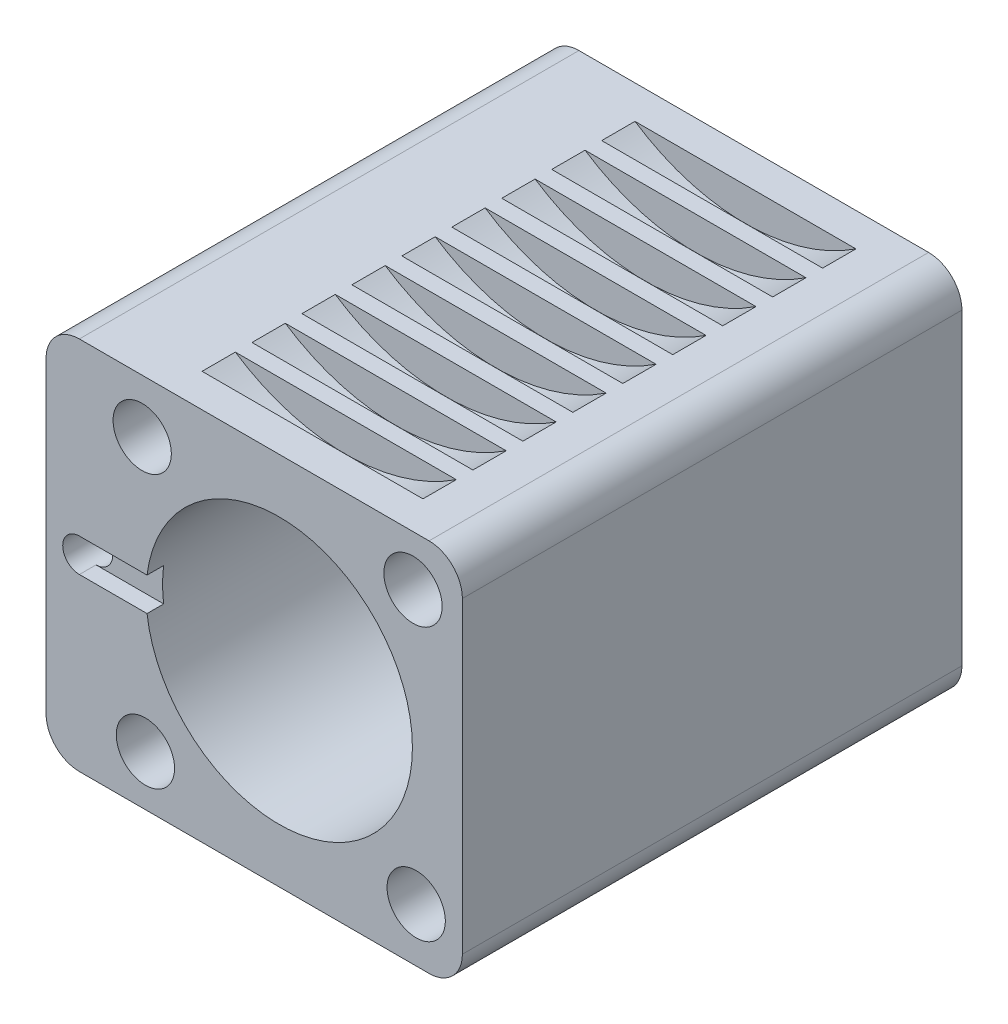
SolidWorks part; units mm, degrees
ref_plane "Front Plane" through (0, 0, 0) normal (0, 0, 1) x (1, 0, 0)
ref_plane "Top Plane" through (0, 0, 0) normal (0, 1, 0) x (1, 0, 0)
ref_plane "Right Plane" through (0, 0, 0) normal (1, 0, 0) x (0, 0, -1)
sketch "Sketch1" plane through (0, 0, 0) normal (0, 0, 1) x (1, 0, 0)
  line L0 (0, 0) -> (20.8284, 21.3284) construction
  line L1 (-24, 22.5) -> (18, 22.5)
  line L2 (-28, 18.5) -> (-28, -18.5)
  line L3 (-24, -22.5) -> (18, -22.5)
  line L4 (22, 18.5) -> (22, -18.5)
  arc A1 (-28, -18.5) -> (-24, -22.5) centre (-24, -18.5) ccw
  arc A2 (18, -22.5) -> (22, -18.5) centre (18, -18.5) ccw
  arc A3 (18, 22.5) -> (22, 18.5) centre (18, 18.5) cw
  arc A4 (-24, 22.5) -> (-28, 18.5) centre (-24, 18.5) ccw
  circle A5 centre (0, 0) radius 16
  circle A6 centre (0, 0) radius 23 construction
  circle A7 centre (16.0694, 16.4552) radius 3.5
  circle A8 centre (16.4552, -16.0694) radius 3.5
  circle A9 centre (-16.0694, -16.4552) radius 3.5
  circle A10 centre (-16.4552, 16.0694) radius 3.5
  circle A11 centre (-24, 0) radius 2
  point P4 (22, 0)
  point P9 (-28, -22.5)
  point P14 (22, 22.5)
  point P17 (-28, 22.5)
  point P33 (0, 0)
  dimension "D3" = 22
  dimension "D4" = 4
  dimension "D5" = 32
  dimension "D6" = 46
  dimension "D7" = 7
  dimension "D10" = 4
  dimension "D1" = 45
  dimension "D2" = 50
  dimension "D9" = 24
  dimension "D8" = 4
extrude "Boss-Extrude1" add sketch "Sketch1" along normal blind 60
sketch "Sketch2" plane through (0, 0, 0) normal (0, 0, -1) x (-1, 0, 0)
  circle A0 centre (0, 0) radius 18
  circle A1 centre (0, 0) radius 16 construction
  circle A2 centre (0, 0) radius 16
  dimension "D1" = 36
extrude "Boss-Extrude2" add sketch "Sketch2" along normal blind 2
sketch "Sketch3" plane through (0, 0, 60) normal (0, 0, 1) x (1, 0, 0)
  line L1 (-15.8745, -2) -> (-24, -2)
  line L3 (-15.8745, 2) -> (-24, 2)
  line L4 (-24, -2) -> (-24, 2)
  circle A0 centre (-24, 0) radius 2 construction
  circle A1 centre (0, 0) radius 16 construction
  circle A2 centre (0, 0) radius 16
  arc A3 (-15.8745, -2) -> (-15.8745, 2) centre (0, 0) cw
  circle M8 centre (-24, 0) radius 2
  circle M9 centre (0, 0) radius 16
  dimension "D1" = 4
extrude "Cut-Extrude1" cut sketch "Sketch3" against normal blind 2 contours L3 L1 M9 M8
sketch "Sketch6" plane through (0, 0, 0) normal (1, 0, 0) x (0, 0, -1)
  line L0 (-60, 22.5) -> (0, 22.5) construction
  line L1 (-56, 42.5) -> (-52, 42.5)
  line L2 (-56, 42.5) -> (-56, 18.5)
  line L3 (-56, 18.5) -> (-52, 18.5)
  line L4 (-52, 42.5) -> (-52, 18.5)
  line L5 (-60, -18.5) -> (-60, 18.5) construction
  dimension "D1" = 24
  dimension "D2" = 4
  dimension "D3" = 4
  dimension "D4" = 4
revolve "Cut-Revolve1" cut sketch "Sketch6" angle 360 about L1
pattern_linear "LPattern1" count 9 spacing 6 along (0, 0, -1) of "Cut-Revolve1"
mirror "Mirror1" about plane through (0, 0, 0) normal (0, 1, 0) of "LPattern1", "Cut-Revolve1"
